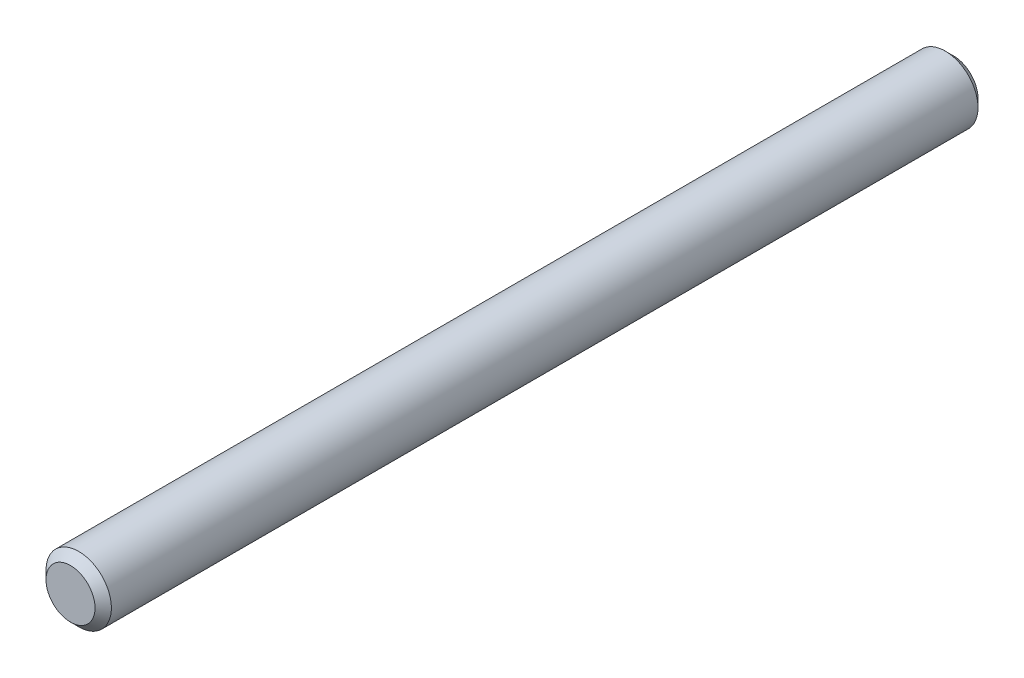
SolidWorks part; units mm, degrees
ref_plane "Plane1" through (0, 0, 0) normal (0, 0, 1) x (1, 0, 0)
ref_plane "Plane2" through (0, 0, 0) normal (0, 1, 0) x (1, 0, 0)
ref_plane "Plane3" through (0, 0, 0) normal (1, 0, 0) x (0, 0, -1)
sketch "Esquisse1" plane through (0, 0, 0) normal (0, 0, 1) x (1, 0, 0)
  circle A0 centre (0, 0) radius 1
  dimension "D1" = 2
extrude "Base-Extrusion" add sketch "Esquisse1" along normal blind 27
chamfer "Chanfrein1" distance 0.25 angle 45
